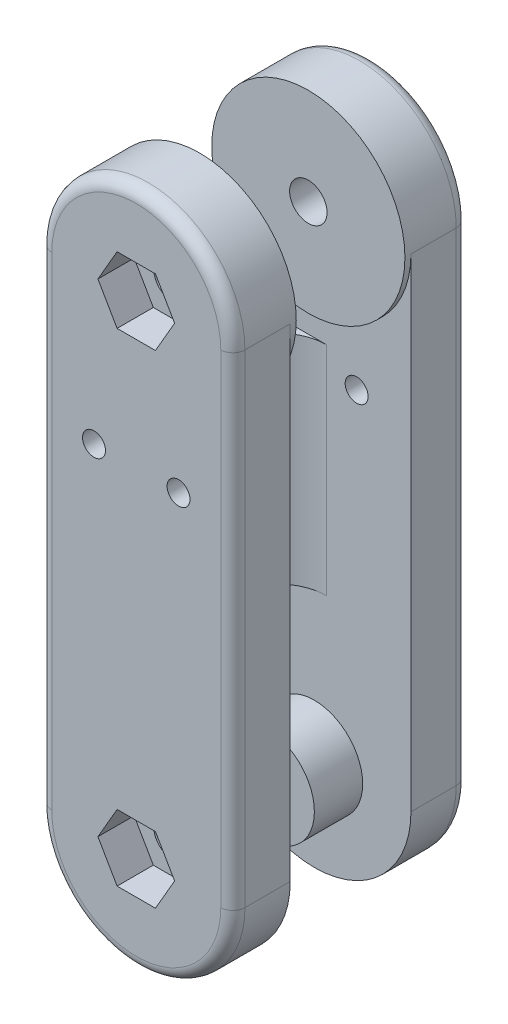
SolidWorks part; units mm, degrees
ref_plane "Front Plane" through (0, 0, 0) normal (0, 0, 1) x (1, 0, 0)
ref_plane "Top Plane" through (0, 0, 0) normal (0, 1, 0) x (1, 0, 0)
ref_plane "Right Plane" through (0, 0, 0) normal (1, 0, 0) x (0, 0, -1)
sketch "Sketch1" plane through (0, 0, 0) normal (0, 0, 1) x (1, 0, 0)
  line L0 (0, 0) -> (0, 40) construction
  line L1 (-8, 0) -> (-8, 40)
  line L2 (8, 0) -> (8, 40)
  arc A0 (-8, 0) -> (8, 0) centre (0, 0) ccw
  arc A1 (8, 40) -> (-8, 40) centre (0, 40) ccw
  circle A2 centre (0, 40) radius 1.55
  circle A3 centre (0, 0) radius 1.55
  point P3 (0, 20)
  dimension "D1" = 3.1
  dimension "D2" = 8
  dimension "D3" = 40
extrude "Boss-Extrude1" add sketch "Sketch1" along normal blind 4.75
fillet "Fillet2" radius 1 4 edges at (-8, 20, 4.75) (0, 48, 4.75) (8, 20, 4.75) (0, -8, 4.75)
sketch "Sketch2" plane through (0, 0, 4.75) normal (0, 0, 1) x (1, 0, 0)
  line L1 (3.1754, 40) -> (1.5877, 42.75)
  line L2 (1.5877, 42.75) -> (-1.5877, 42.75)
  line L3 (-1.5877, 42.75) -> (-3.1754, 40)
  line L4 (-3.1754, 40) -> (-1.5877, 37.25)
  line L5 (-1.5877, 37.25) -> (1.5877, 37.25)
  line L6 (1.5877, 37.25) -> (3.1754, 40)
  line L7 (3.1754, 0) -> (1.5877, 2.75)
  line L8 (1.5877, 2.75) -> (-1.5877, 2.75)
  line L9 (-1.5877, 2.75) -> (-3.1754, 0)
  line L10 (-3.1754, 0) -> (-1.5877, -2.75)
  line L11 (-1.5877, -2.75) -> (1.5877, -2.75)
  line L12 (1.5877, -2.75) -> (3.1754, 0)
  circle A0 centre (0, 40) radius 2.75 construction
  circle A1 centre (0, 0) radius 2.75 construction
  dimension "D1" = 5.5
extrude "Cut-Extrude1" cut sketch "Sketch2" against normal blind 3
sketch "Sketch3" plane through (0, 0, 0) normal (0, 0, -1) x (-1, 0, 0)
  line L0 (8, 40) -> (8, 0) construction
  line L1 (8, 30) -> (3, 30)
  line L2 (8, 30) -> (8, 12)
  line L3 (8, 12) -> (3, 12)
  line L4 (3, 30) -> (3, 12) construction
  line L5 (3, 30) -> (3, 12)
  circle A0 centre (0, 40) radius 1.55 construction
  circle A1 centre (0, 0) radius 1.55 construction
  dimension "D1" = 5
  dimension "D2" = 10
  dimension "D3" = 12
extrude "Boss-Extrude2" add sketch "Sketch3" along normal blind 5
sketch "Sketch8" plane through (0, 0, 0) normal (0, 0, -1) x (-1, 0, 0)
  circle A0 centre (0, 0) radius 4
  circle A1 centre (0, 0) radius 1.55
  dimension "D1" = 8
extrude "Boss-Extrude4" add sketch "Sketch8" along normal blind 4
sketch "Sketch9" plane through (0, 0, 0) normal (0, 0, -1) x (-1, 0, 0)
  circle A0 centre (0, 40) radius 8
  circle A1 centre (0, 40) radius 1.55
  dimension "D1" = 3.1
extrude "Boss-Extrude5" add sketch "Sketch9" along normal blind 0.5
fillet "Fillet3" radius 4 1 edges at (-3, 21, 0)
mirror "Mirror5" about plane through (0, 0, -5) normal (0, 0, 1) of bodies 113 103
sketch "Sketch6" plane through (0, 0, -14.75) normal (0, 0, -1) x (-1, 0, 0)
  line L0 (0, 42.75) -> (0, 45.4685) construction
  line L1 (-6.725, 42) -> (-5.525, 42)
  line L2 (-6.725, 42) -> (-6.725, 36)
  line L3 (-6.725, 36) -> (-5.525, 36)
  line L4 (-5.525, 42) -> (-5.525, 36)
  line L10 (0, 40) -> (5.2045, 40) construction
  line L11 (5.525, 42) -> (5.525, 36)
  line L12 (6.725, 36) -> (5.525, 36)
  line L13 (6.725, 42) -> (6.725, 36)
  line L14 (6.725, 42) -> (5.525, 42)
  dimension "D1" = 11.05
  dimension "D2" = 1.2
  dimension "D3" = 6
  dimension "D4" = 2
extrude "Boss-Extrude3" [suppressed] add sketch "Sketch6" along normal blind 4
chamfer "Chamfer1" [suppressed] distance 1.5 angle 45
ref_plane "Plane1" through (0, 0, -5) normal (0, 0, -1) x (-1, 0, 0)
sketch "Sketch7" plane through (0, 0, -14.75) normal (0, 0, -1) x (-1, 0, 0)
  line L0 (0, 40) -> (0, 18.9568) construction
  circle A0 centre (-3.5, 28) radius 0.95
  circle A1 centre (0, 40) radius 1.55 construction
  circle A2 centre (3.5, 28) radius 0.95
  dimension "D1" = 1.9
  dimension "D2" = 7
  dimension "D3" = 12
extrude "Cut-Extrude3" cut sketch "Sketch7" against normal through all
